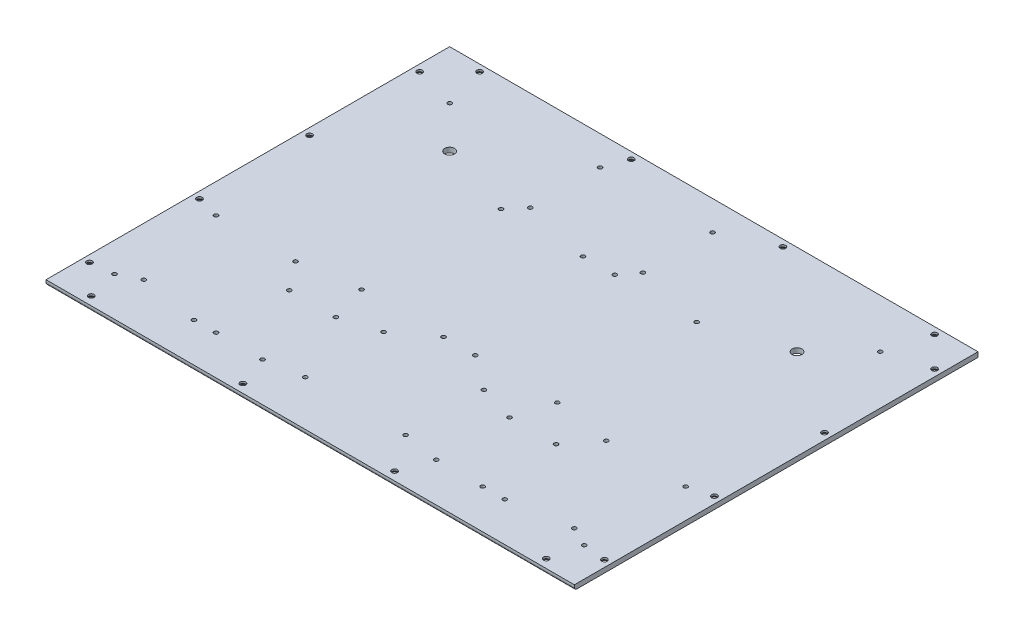
SolidWorks part; units mm, degrees
material "3.3523 (EN-AW 5052)"
ref_plane "前基準面" through (0, 0, 0) normal (0, 0, 1) x (1, 0, 0)
ref_plane "上基準面" through (0, 0, 0) normal (0, 1, 0) x (1, 0, 0)
ref_plane "右基準面" through (0, 0, 0) normal (1, 0, 0) x (0, 0, -1)
sketch "草圖2" plane through (0, 0, 0) normal (0, 1, 0) x (1, 0, 0)
  line L1 (0, 0) -> (432, 0)
  line L2 (0, 0) -> (0, 330)
  line L3 (0, 330) -> (432, 330)
  line L4 (432, 0) -> (432, 330)
  dimension "D1" = 330
  dimension "D2" = 432
extrude "填料-伸長1" add sketch "草圖2" along normal blind 4
hole_wizard "側板連接" positions "草圖4" profile "草圖3" countersink size "M4" standard "ISO" end condition through all
sketch "草圖4" plane through (0, 0, 0) normal (0, 1, 0) x (1, 0, 0)
  line L0 (0, 330) -> (0, 0) construction
  line L2 (432, 330) -> (0, 330) construction
  line L3 (0, 0) -> (432, 0) construction
  line L4 (432, 0) -> (432, 330) construction
  point P0 (30, 7)
  point P1 (5.5, 300)
  point P3 (5.5, 210)
  point P5 (5.5, 120)
  point P7 (5.5, 30)
  point P9 (154, 7)
  point P11 (278, 7)
  point P13 (402, 7)
  point P15 (426.5, 30)
  point P17 (426.5, 120)
  point P19 (426.5, 210)
  point P21 (426.5, 300)
  point P23 (402, 324.5)
  point P25 (278, 324.5)
  point P27 (154, 324.5)
  point P29 (30, 324.5)
  dimension "D1" = 30
  dimension "D2" = 124
  dimension "D3" = 124
  dimension "D4" = 124
  dimension "D5" = 30
  dimension "D6" = 90
  dimension "D7" = 90
  dimension "D8" = 90
  dimension "D9" = 30
  dimension "D10" = 124
  dimension "D11" = 124
  dimension "D12" = 124
  dimension "D13" = 30
  dimension "D14" = 90
  dimension "D15" = 90
  dimension "D16" = 90
  dimension "D17" = 5.5
  dimension "D18" = 5.5
  dimension "D19" = 5.5
  dimension "D20" = 7
sketch "草圖3" plane through (30, 0, -7) normal (1, 0, 0) x (0, 0, -1)
  line L0 (0, 0) -> (0, 4)
  line L1 (0, 4) -> (2.25, 4)
  line L2 (2.25, 4) -> (2.25, 2.45)
  line L3 (2.25, 2.45) -> (4.7, 0)
  line L5 (4.7, 0) -> (0, 0)
  line L6 (-2.25, 2.45) -> (-4.7, 0) construction
  line L11 (0, -6.35) -> (0, 107.95) construction
  dimension "貫穿孔直徑" = 4.5
  dimension "貫穿孔深度" = 4
  dimension "近端錐孔直徑" = 9.4
  dimension "近端錐孔角度" = 90
fillet "圓角1" radius 2 1 edges at (216, 0, 0)
hole_wizard "變壓器" positions "草圖5" profile "草圖6" hole size "Ø8.0" standard "ISO" end condition through all
sketch "草圖5" plane through (0, 0, 0) normal (0, -1, 0) x (-1, 0, 0)
  line L0 (-432, 330) -> (0, 330) construction
  line L1 (0, 330) -> (0, 2) construction
  line L2 (-432, 2) -> (-432, 330) construction
  point P0 (-74, 256)
  point P2 (-358, 256)
  dimension "D1" = 74
  dimension "D2" = 74
  dimension "D3" = 74
  dimension "D4" = 74
sketch "草圖6" plane through (74, 0, -256) normal (1, 0, 0) x (0, 0, -1)
  line L0 (0, 0) -> (0, 4)
  line L1 (0, 4) -> (4, 4)
  line L2 (4, 4) -> (4, 0)
  line L5 (4, 0) -> (0, 0)
  line L11 (0, -6.35) -> (0, 107.95) construction
  dimension "貫穿孔直徑" = 8
  dimension "貫穿孔深度" = 4
hole_wizard "M4P8" positions "草圖7" profile "草圖8" hole size "M4" standard "ISO" end condition through all
sketch "草圖7" plane through (0, 0, 0) normal (0, -1, 0) x (-1, 0, 0)
  line L0 (0, 330) -> (0, 2) construction
  line L1 (0, 0) -> (-432, 0) construction
  line L3 (-432, 330) -> (0, 330) construction
  line L4 (0, 330) -> (0, 2) construction
  line L5 (-432, 2) -> (-432, 330) construction
  point P0 (-107, 32)
  point P2 (-107, 92)
  point P4 (-145, 32)
  point P6 (-145, 92)
  point P8 (-287, 32)
  point P10 (-287, 92)
  point P12 (-325, 32)
  point P14 (-325, 92)
  point P16 (-147, 249)
  point P18 (-239, 249)
  point P20 (-147, 306)
  point P22 (-239, 306)
  dimension "D1" = 107
  dimension "D2" = 38
  dimension "D3" = 60
  dimension "D4" = 32
  dimension "D5" = 57
  dimension "D6" = 24
  dimension "D7" = 92
  dimension "D8" = 147
  dimension "D9" = 38
  dimension "D10" = 107
sketch "草圖8" plane through (107, 0, -32) normal (1, 0, 0) x (0, 0, -1)
  line L0 (0, 0) -> (0, 4)
  line L1 (0, 4) -> (1.65, 4)
  line L2 (1.65, 4) -> (1.65, 0)
  line L5 (1.65, 0) -> (0, 0)
  line L11 (0, -6.35) -> (0, 107.95) construction
  dimension "貫穿孔直徑" = 3.3
  dimension "貫穿孔深度" = 4
hole_wizard "腳座" positions "草圖9" profile "草圖10" tap size "M4" standard "ISO" end condition through all
sketch "草圖9" plane through (0, 0, 0) normal (0, -1, 0) x (-1, 0, 0)
  line L0 (0, 0) -> (-432, 0) construction
  line L1 (0, 330) -> (0, 2) construction
  line L2 (-432, 2) -> (-432, 330) construction
  line L3 (-432, 330) -> (0, 330) construction
  point P0 (-40, 40)
  point P2 (-40, 290)
  point P4 (-392, 290)
  point P6 (-392, 40)
  dimension "D1" = 40
  dimension "D2" = 40
  dimension "D3" = 40
  dimension "D4" = 40
  dimension "D5" = 40
sketch "草圖10" plane through (40, 0, -40) normal (1, 0, 0) x (0, 0, -1)
  line L0 (0, 0) -> (0, 4)
  line L1 (0, 4) -> (1.65, 4)
  line L2 (1.65, 4) -> (1.65, 0.375)
  line L3 (1.65, 0.375) -> (2.025, 0)
  line L5 (2.025, 0) -> (0, 0)
  line L6 (-1.65, 0.375) -> (-2.025, 0) construction
  line L11 (0, -6.35) -> (0, 107.95) construction
  dimension "貫穿螺孔鑽直徑" = 3.3
  dimension "貫穿螺孔鑽深度" = 4
  dimension "近端錐孔直徑" = 4.05
  dimension "近端錐孔角度" = 90
cosmetic thread "鑽孔螺紋21"
cosmetic thread "鑽孔螺紋22"
cosmetic thread "鑽孔螺紋23"
cosmetic thread "鑽孔螺紋24"
hole_wizard "M4P9" positions "草圖11" profile "草圖12" hole size "M4" standard "ISO" end condition through all
sketch "草圖11" plane through (0, 0, 0) normal (0, -1, 0) x (-1, 0, 0)
  line L0 (0, 0) -> (-432, 0) construction
  line L1 (0, 330) -> (0, 2) construction
  line L2 (-432, 2) -> (-432, 330) construction
  point P0 (-24, 32)
  point P2 (-89, 32)
  point P4 (-24, 115)
  point P6 (-89, 115)
  point P8 (-136, 122)
  point P10 (-136, 236)
  point P12 (-203, 122)
  point P14 (-203, 236)
  point P16 (-229, 122)
  point P18 (-229, 236)
  point P20 (-296, 122)
  point P22 (-296, 236)
  point P24 (-343, 32)
  point P26 (-408, 32)
  point P28 (-408, 115)
  point P30 (-343, 115)
  dimension "D1" = 32
  dimension "D2" = 65
  dimension "D3" = 83
  dimension "D4" = 24
  dimension "D5" = 24
  dimension "D6" = 65
  dimension "D7" = 67
  dimension "D8" = 136
  dimension "D9" = 67
  dimension "D10" = 136
  dimension "D11" = 114
  dimension "D12" = 122
sketch "草圖12" plane through (24, 0, -32) normal (1, 0, 0) x (0, 0, -1)
  line L0 (0, 0) -> (0, 4)
  line L1 (0, 4) -> (1.65, 4)
  line L2 (1.65, 4) -> (1.65, 0)
  line L5 (1.65, 0) -> (0, 0)
  line L11 (0, -6.35) -> (0, 107.95) construction
  dimension "貫穿孔直徑" = 3.3
  dimension "貫穿孔深度" = 4
hole_wizard "M4P10" positions "草圖13" profile "草圖14" hole size "M4" standard "ISO" end condition through all
sketch "草圖13" plane through (0, 0, 0) normal (0, -1, 0) x (-1, 0, 0)
  line L0 (-432, 2) -> (-432, 330) construction
  line L1 (0, 0) -> (-432, 0) construction
  line L2 (0, 330) -> (0, 2) construction
  point P0 (-175, 37)
  point P2 (-257, 37)
  point P4 (-257, 101)
  point P6 (-175, 101)
  dimension "D1" = 175
  dimension "D2" = 64
  dimension "D3" = 37
  dimension "D4" = 175
sketch "草圖14" plane through (175, 0, -37) normal (1, 0, 0) x (0, 0, -1)
  line L0 (0, 0) -> (0, 4)
  line L1 (0, 4) -> (1.65, 4)
  line L2 (1.65, 4) -> (1.65, 0)
  line L5 (1.65, 0) -> (0, 0)
  line L11 (0, -6.35) -> (0, 107.95) construction
  dimension "貫穿孔直徑" = 3.3
  dimension "貫穿孔深度" = 4
